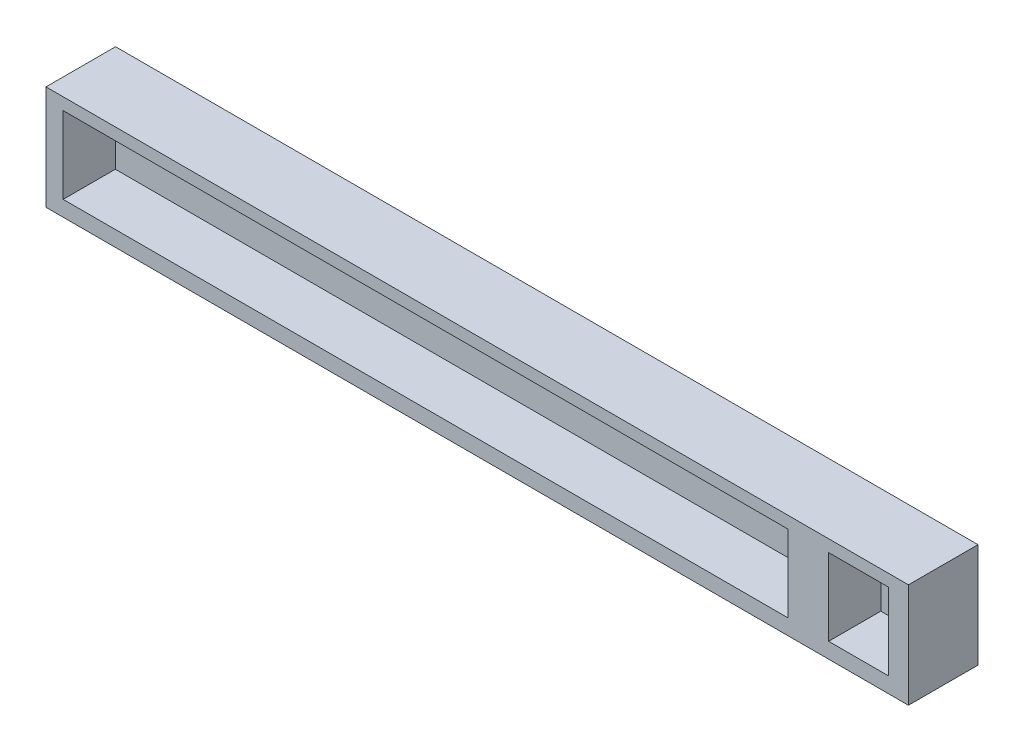
SolidWorks part; units mm, degrees
material "Glas"
ref_plane "Ebene vorne" through (0, 0, 0) normal (0, 0, 1) x (1, 0, 0)
ref_plane "Ebene oben" through (0, 0, 0) normal (0, 1, 0) x (1, 0, 0)
ref_plane "Ebene rechts" through (0, 0, 0) normal (1, 0, 0) x (0, 0, -1)
sketch "Skizze3" plane through (0, 0, 0) normal (0, 0, 1) x (1, 0, 0)
  line L1 (0, 0) -> (248, 0)
  line L2 (0, 0) -> (0, 30)
  line L3 (0, 30) -> (248, 30)
  line L4 (248, 0) -> (248, 30)
  dimension "D1" = 248
  dimension "D2" = 30
extrude "Aufsatz-Linear austragen2" add sketch "Skizze3" along normal blind 20 contours L3 L4 L1 L2
sketch "Skizze4" plane through (0, 0, 20) normal (0, 0, 1) x (1, 0, 0)
  line L0 (218, 45.8183) -> (218, -15.8183) construction
  line L1 (0, 0) -> (0, 30) construction
  line L3 (242.2706, 26.5597) -> (225.0468, 26.5597)
  line L4 (242.2706, 26.5597) -> (242.2706, 4.4558)
  line L5 (242.2706, 4.4558) -> (225.0468, 4.4558)
  line L6 (225.0468, 26.5597) -> (225.0468, 4.4558)
  line L7 (213.4304, 26.5597) -> (4.9374, 26.5597)
  line L8 (213.4304, 26.5597) -> (213.4304, 4.4558)
  line L9 (213.4304, 4.4558) -> (4.9374, 4.4558)
  line L10 (4.9374, 26.5597) -> (4.9374, 4.4558)
  line L11 (0, 30) -> (248, 30) construction
  line L12 (0, 0) -> (248, 0) construction
  dimension "D1" = 218
  dimension "D2" = 208.493
  dimension "D3" = 17.2238
  dimension "D4" = 22.1039
  dimension "D5" = 11.6163
  dimension "D6" = 4.9374
  dimension "D7" = 3.4403
  dimension "D8" = 4.4558
  dimension "D9" = 4.4558
extrude "Schnitt-Linear austragen1" cut sketch "Skizze4" against normal blind 15
